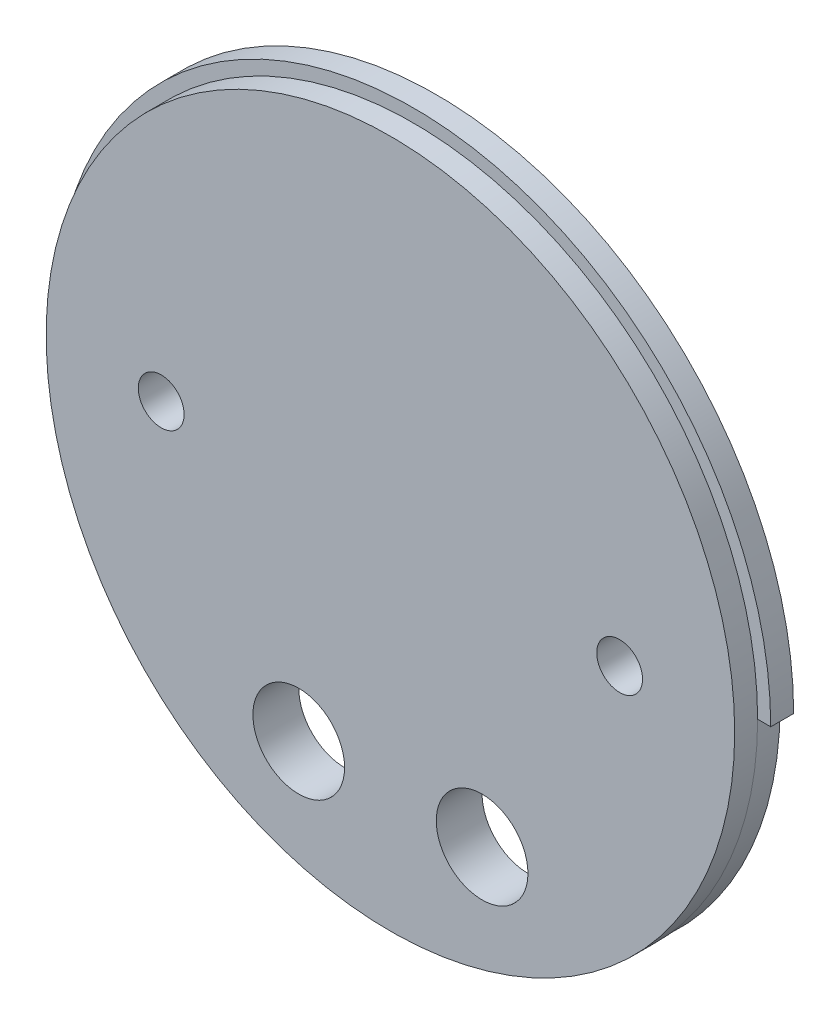
SolidWorks part; units mm, degrees
ref_plane "Front Plane" through (0, 0, 0) normal (0, 0, 1) x (1, 0, 0)
ref_plane "Top Plane" through (0, 0, 0) normal (0, 1, 0) x (1, 0, 0)
ref_plane "Right Plane" through (0, 0, 0) normal (1, 0, 0) x (0, 0, -1)
sketch "Sketch1" plane through (0, 0, 0) normal (0, 0, 1) x (1, 0, 0)
  circle A0 centre (0, 0) radius 49.5046
  dimension "D1" = 99.0092
extrude "Boss-Extrude1" add sketch "Sketch1" along normal blind 3.175
sketch "Sketch2" plane through (0, 0, 3.175) normal (0, 0, 1) x (1, 0, 0)
  circle A0 centre (0, 0) radius 47.6885
  dimension "D1" = 95.377
extrude "Boss-Extrude2" add sketch "Sketch2" along normal blind 3.175
sketch "Sketch3" plane through (0, 0, 6.35) normal (0, 0, 1) x (1, 0, 0)
  line L0 (-7.9375, -31.2354) -> (7.9375, -31.2354) construction
  circle A0 centre (-31.75, 0) radius 3.175
  circle A1 centre (31.75, 0) radius 3.175
  circle A2 centre (-12.7, -31.2354) radius 6.35
  circle A3 centre (-12.7, -31.2354) radius 13.97 construction
  circle A4 centre (-12.7, -31.2354) radius 4.7625 construction
  circle A5 centre (0, 0) radius 47.6885 construction
  circle A6 centre (12.7, -31.2354) radius 6.35
  circle A7 centre (12.7, -31.2354) radius 13.97 construction
  circle A8 centre (-12.7, -31.2354) radius 12.7 construction
  circle A9 centre (12.7, -31.2354) radius 12.7 construction
  circle A10 centre (12.7, -31.2354) radius 4.7625 construction
  dimension "D1" = 6.35
  dimension "D2" = 6.35
  dimension "D5" = 12.7
  dimension "D6" = 27.94
  dimension "D7" = 12.7
  dimension "D8" = 27.94
  dimension "D9" = 25.4
  dimension "D10" = 25.4
  dimension "D11" = 9.525
  dimension "D12" = 9.525
  dimension "D3" = 63.5
  dimension "D4" = 31.75
extrude "Cut-Extrude1" cut sketch "Sketch3" against normal through all
sketch "Sketch4" plane through (0, 0, 3.175) normal (0, 0, 1) x (1, 0, 0)
  line L0 (-50.165, 0) -> (-47.625, 0)
  line L1 (47.625, 0) -> (50.165, 0)
  arc A0 (-50.165, 0) -> (50.165, 0) centre (0, 0) ccw
  arc A1 (-47.625, 0) -> (47.625, 0) centre (0, 0) ccw
extrude "Cut-Extrude2" cut sketch "Sketch4" against normal through all
